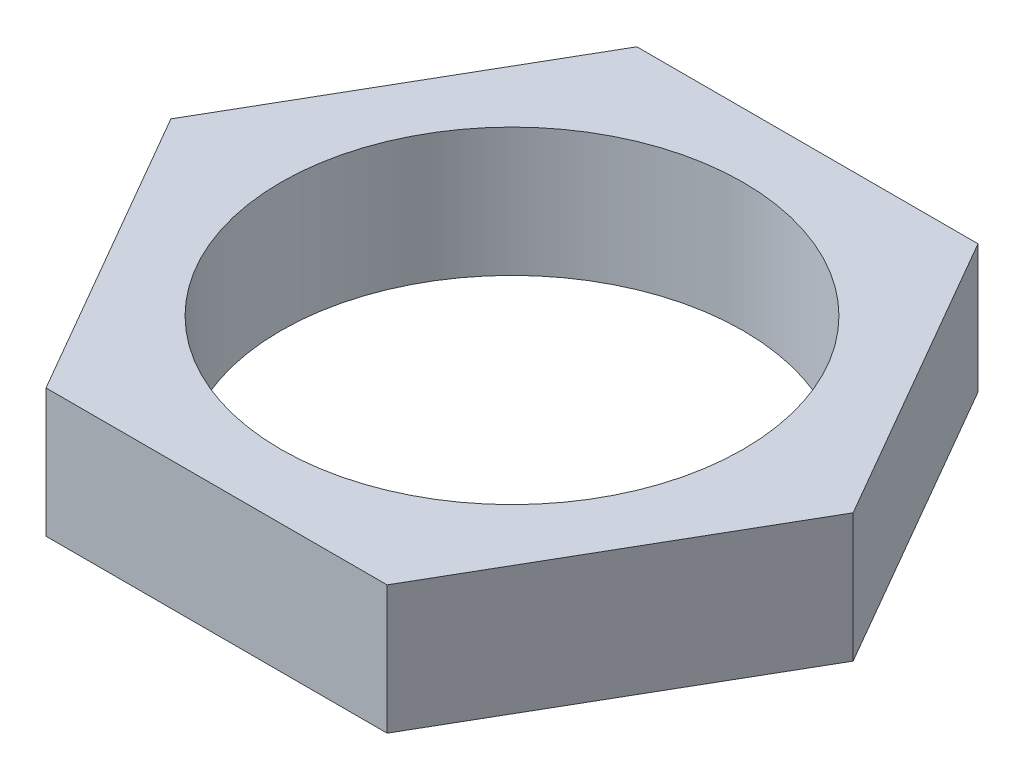
SolidWorks part; units mm, degrees
material "1060 Alloy"
ref_plane "Front Plane" through (0, 0, 0) normal (0, 0, 1) x (1, 0, 0)
ref_plane "Top Plane" through (0, 0, 0) normal (0, 1, 0) x (1, 0, 0)
ref_plane "Right Plane" through (0, 0, 0) normal (1, 0, 0) x (0, 0, -1)
sketch "Sketch1" plane through (0, 0, 0) normal (0, 1, 0) x (1, 0, 0)
  line L1 (13.2791, 0) -> (6.6395, 11.5)
  line L2 (6.6395, 11.5) -> (-6.6395, 11.5)
  line L3 (-6.6395, 11.5) -> (-13.2791, 0)
  line L4 (-13.2791, 0) -> (-6.6395, -11.5)
  line L5 (-6.6395, -11.5) -> (6.6395, -11.5)
  line L6 (6.6395, -11.5) -> (13.2791, 0)
  circle A0 centre (0, 0) radius 11.5 construction
  circle A1 centre (0, 0) radius 9
  dimension "D2" = 18
  dimension "D1" = 23
extrude "Boss-Extrude1" add sketch "Sketch1" along normal blind 5
